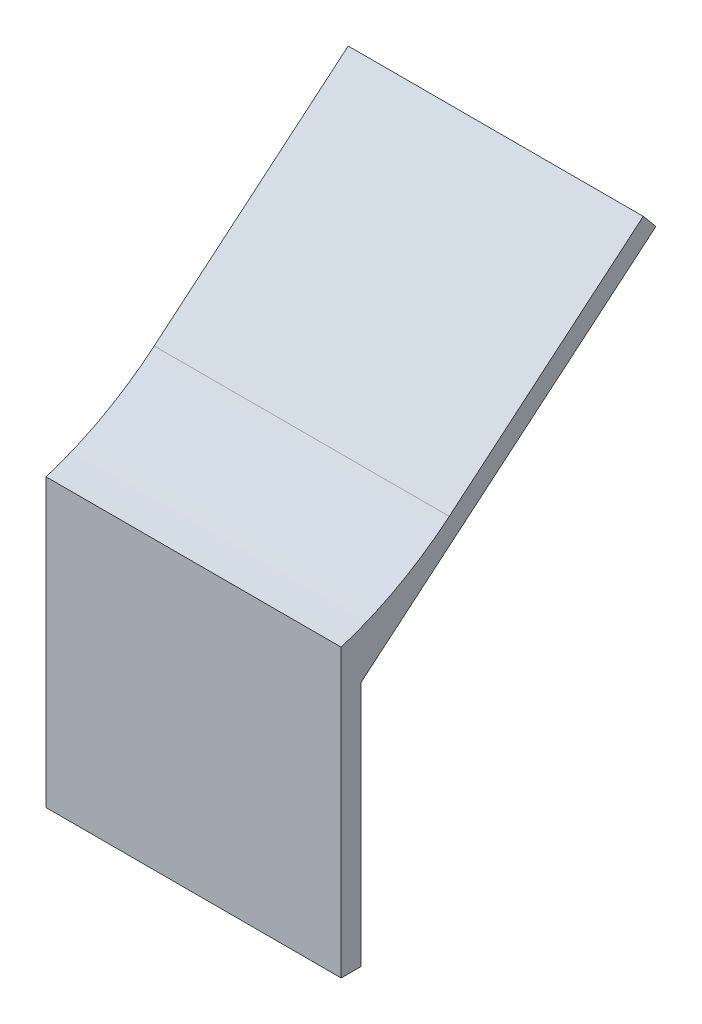
SolidWorks part; units mm, degrees
ref_plane "Front Plane" through (0, 0, 0) normal (0, 0, 1) x (1, 0, 0)
ref_plane "Top Plane" through (0, 0, 0) normal (0, 1, 0) x (1, 0, 0)
ref_plane "Right Plane" through (0, 0, 0) normal (1, 0, 0) x (0, 0, -1)
sketch "Sketch1" plane through (0, 0, 0) normal (1, 0, 0) x (0, 0, -1)
  line L0 (0, 0) -> (0, 29.1306)
  line L1 (10.9902, 35.1545) -> (30.7144, 51.7051)
  line L2 (30.7144, 51.7051) -> (32, 50.173)
  line L3 (32, 50.173) -> (2, 25)
  line L4 (2, 25) -> (2, 0)
  line L5 (2, 0) -> (0, 0)
  line L6 (0, 0) -> (-62.9582, 0) construction
  arc A0 (0, 29.1306) -> (10.9902, 35.1545) centre (-9.6167, 59.7128) ccw
  point P8 (-0.1772, 0)
  point P10 (91.6659, 101.9614)
  point P12 (0, 22.624)
  point P13 (3.1076, 17.0671)
  point P14 (2, 26.5097)
  point P15 (0, 29.1306)
  dimension "D1" = 140
  dimension "D2" = 30
  dimension "D3" = 2
  dimension "D4" = 2
  dimension "D5" = 25
extrude "Boss-Extrude1" add sketch "Sketch1" along normal blind 30
